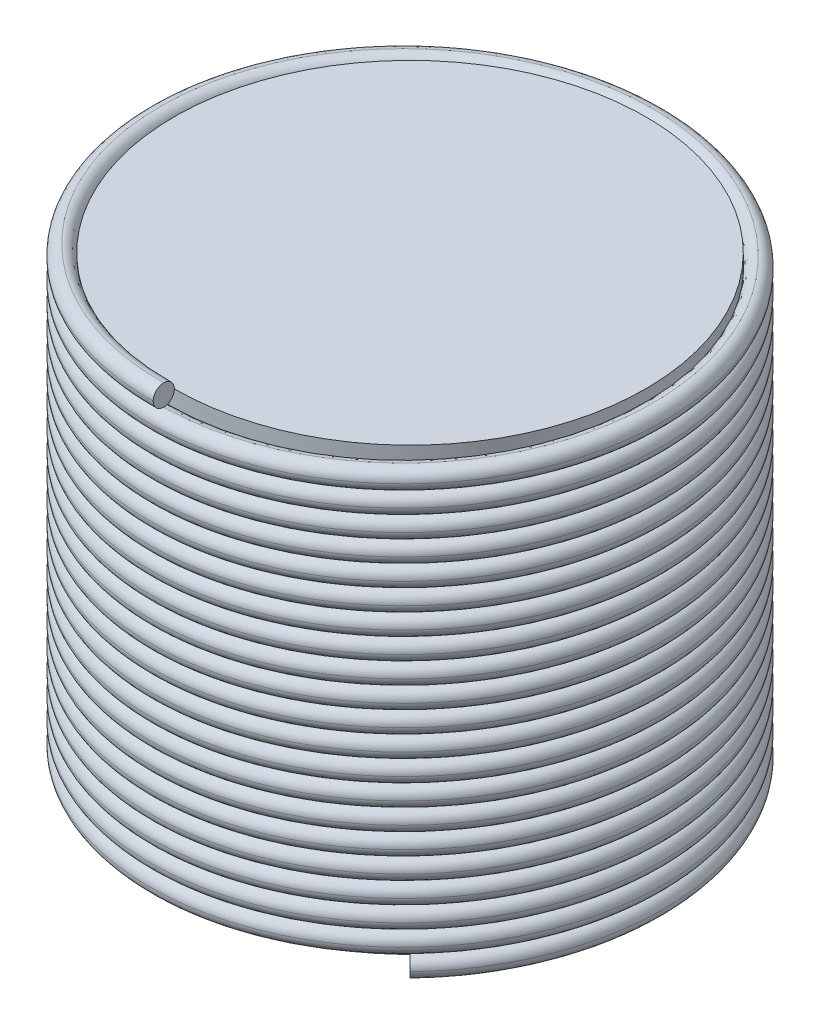
SolidWorks part; units mm, degrees
ref_plane "Front Plane" through (0, 0, 0) normal (0, 0, 1) x (1, 0, 0)
ref_plane "Top Plane" through (0, 0, 0) normal (0, 1, 0) x (1, 0, 0)
ref_plane "Right Plane" through (0, 0, 0) normal (1, 0, 0) x (0, 0, -1)
sketch "Base" plane through (0, 0, 0) normal (0, 1, 0) x (1, 0, 0)
  line L0 (0, 0) -> (0, 12.0382) construction
  line L1 (0, 0) -> (16.2312, 0) construction
  circle A0 centre (0, 0) radius 8.925
  dimension "D1" = 17.85
extrude "Boss-Extrude1" add sketch "Base" along normal blind 16.7 contours A0
sketch "Helix" plane through (0, 16.7, 0) normal (0, 1, 0) x (1, 0, 0)
  circle A0 centre (0, 0) radius 9.325
  circle A1 centre (0, 0) radius 8.925 construction
  dimension "D1" = 0.4
curve "Helix/Spiral1" pitch 0.8 height 16.7 turns 20.875
ref_plane "Start" through (0, 0, 0) normal (1, 0, 0) x (0, 0, -1)
sketch "Winding" plane through (0, 0, 0) normal (1, 0, 0) x (0, 0, -1)
  line L5 (-4.3372, 16.7) -> (-7.5224, 16.7) construction
  line L6 (8.925, 16.7) -> (-8.925, 16.7) construction
  circle A0 centre (-9.325, 16.7) radius 0.4
  spline S0 degree 3 poles (-9.325, 16.7) (-9.325, 16.6834) (-8.8395, 16.65) (-6.7654, 16.6) (-3.6614, 16.55) (0, 16.5) (3.6614, 16.45) (6.7654, 16.4) (8.8395, 16.35) (9.5678, 16.3) (8.8395, 16.25) (6.7654, 16.2) (2.6268, 16.1333) (-2.6268, 16.0667) (-6.7654, 16) (-8.8395, 15.95) (-9.5678, 15.9) (-8.8395, 15.85) (-6.7654, 15.8) (-2.6268, 15.7333) (2.6268, 15.6667) (6.7654, 15.6) (8.8395, 15.55) (9.5678, 15.5) (8.8395, 15.45) (6.7654, 15.4) (2.6268, 15.3333) (-2.6268, 15.2667) (-6.7654, 15.2) (-8.8395, 15.15) (-9.5678, 15.1) (-8.8395, 15.05) (-6.7654, 15) (-2.6268, 14.9333) (2.6268, 14.8667) (6.7654, 14.8) (8.8395, 14.75) (9.5678, 14.7) (8.8395, 14.65) (6.7654, 14.6) (2.6268, 14.5333) (-2.6268, 14.4667) (-6.7654, 14.4) (-8.8395, 14.35) (-9.5678, 14.3) (-8.8395, 14.25) (-6.7654, 14.2) (-2.6268, 14.1333) (2.6268, 14.0667) (6.7654, 14) (8.8395, 13.95) (9.5678, 13.9) (8.8395, 13.85) (6.7654, 13.8) (2.6268, 13.7333) (-2.6268, 13.6667) (-6.7654, 13.6) (-8.8395, 13.55) (-9.5678, 13.5) (-8.8395, 13.45) (-6.7654, 13.4) (-2.6268, 13.3333) (2.6268, 13.2667) (6.7654, 13.2) (8.8395, 13.15) (9.5678, 13.1) (8.8395, 13.05) (6.7654, 13) (2.6268, 12.9333) (-2.6268, 12.8667) (-6.7654, 12.8) (-8.8395, 12.75) (-9.5678, 12.7) (-8.8395, 12.65) (-6.7654, 12.6) (-2.6268, 12.5333) (2.6268, 12.4667) (6.7654, 12.4) (8.8395, 12.35) (9.5678, 12.3) (8.8395, 12.25) (6.7654, 12.2) (2.6268, 12.1333) (-2.6268, 12.0667) (-6.7654, 12) (-8.8395, 11.95) (-9.5678, 11.9) (-8.8395, 11.85) (-6.7654, 11.8) (-2.6268, 11.7333) (2.6268, 11.6667) (6.7654, 11.6) (8.8395, 11.55) (9.5678, 11.5) (8.8395, 11.45) (6.7654, 11.4) (2.6268, 11.3333) (-2.6268, 11.2667) (-6.7654, 11.2) (-8.8395, 11.15) (-9.5678, 11.1) (-8.8395, 11.05) (-6.7654, 11) (-2.6268, 10.9333) (2.6268, 10.8667) (6.7654, 10.8) (8.8395, 10.75) (9.5678, 10.7) (8.8395, 10.65) (6.7654, 10.6) (2.6268, 10.5333) (-2.6268, 10.4667) (-6.7654, 10.4) (-8.8395, 10.35) (-9.5678, 10.3) (-8.8395, 10.25) (-6.7654, 10.2) (-2.6268, 10.1333) (2.6268, 10.0667) (6.7654, 10) (8.8395, 9.95) (9.5678, 9.9) (8.8395, 9.85) (6.7654, 9.8) (2.6268, 9.7333) (-2.6268, 9.6667) (-6.7654, 9.6) (-8.8395, 9.55) (-9.5678, 9.5) (-8.8395, 9.45) (-6.7654, 9.4) (-2.6268, 9.3333) (2.6268, 9.2667) (6.7654, 9.2) (8.8395, 9.15) (9.5678, 9.1) (8.8395, 9.05) (6.7654, 9) (2.6268, 8.9333) (-2.6268, 8.8667) (-6.7654, 8.8) (-8.8395, 8.75) (-9.5678, 8.7) (-8.8395, 8.65) (-6.7654, 8.6) (-2.6268, 8.5333) (2.6268, 8.4667) (6.7654, 8.4) (8.8395, 8.35) (9.5678, 8.3) (8.8395, 8.25) (6.7654, 8.2) (2.6268, 8.1333) (-2.6268, 8.0667) (-6.7654, 8) (-8.8395, 7.95) (-9.5678, 7.9) (-8.8395, 7.85) (-6.7654, 7.8) (-2.6268, 7.7333) (2.6268, 7.6667) (6.7654, 7.6) (8.8395, 7.55) (9.5678, 7.5) (8.8395, 7.45) (6.7654, 7.4) (2.6268, 7.3333) (-2.6268, 7.2667) (-6.7654, 7.2) (-8.8395, 7.15) (-9.5678, 7.1) (-8.8395, 7.05) (-6.7654, 7) (-2.6268, 6.9333) (2.6268, 6.8667) (6.7654, 6.8) (8.8395, 6.75) (9.5678, 6.7) (8.8395, 6.65) (6.7654, 6.6) (2.6268, 6.5333) (-2.6268, 6.4667) (-6.7654, 6.4) (-8.8395, 6.35) (-9.5678, 6.3) (-8.8395, 6.25) (-6.7654, 6.2) (-2.6268, 6.1333) (2.6268, 6.0667) (6.7654, 6) (8.8395, 5.95) (9.5678, 5.9) (8.8395, 5.85) (6.7654, 5.8) (2.6268, 5.7333) (-2.6268, 5.6667) (-6.7654, 5.6) (-8.8395, 5.55) (-9.5678, 5.5) (-8.8395, 5.45) (-6.7654, 5.4) (-2.6268, 5.3333) (2.6268, 5.2667) (6.7654, 5.2) (8.8395, 5.15) (9.5678, 5.1) (8.8395, 5.05) (6.7654, 5) (2.6268, 4.9333) (-2.6268, 4.8667) (-6.7654, 4.8) (-8.8395, 4.75) (-9.5678, 4.7) (-8.8395, 4.65) (-6.7654, 4.6) (-2.6268, 4.5333) (2.6268, 4.4667) (6.7654, 4.4) (8.8395, 4.35) (9.5678, 4.3) (8.8395, 4.25) (6.7654, 4.2) (2.6268, 4.1333) (-2.6268, 4.0667) (-6.7654, 4) (-8.8395, 3.95) (-9.5678, 3.9) (-8.8395, 3.85) (-6.7654, 3.8) (-2.6268, 3.7333) (2.6268, 3.6667) (6.7654, 3.6) (8.8395, 3.55) (9.5678, 3.5) (8.8395, 3.45) (6.7654, 3.4) (2.6268, 3.3333) (-2.6268, 3.2667) (-6.7654, 3.2) (-8.8395, 3.15) (-9.5678, 3.1) (-8.8395, 3.05) (-6.7654, 3) (-2.6268, 2.9333) (2.6268, 2.8667) (6.7654, 2.8) (8.8395, 2.75) (9.5678, 2.7) (8.8395, 2.65) (6.7654, 2.6) (2.6268, 2.5333) (-2.6268, 2.4667) (-6.7654, 2.4) (-8.8395, 2.35) (-9.5678, 2.3) (-8.8395, 2.25) (-6.7654, 2.2) (-2.6268, 2.1333) (2.6268, 2.0667) (6.7654, 2) (8.8395, 1.95) (9.5678, 1.9) (8.8395, 1.85) (6.7654, 1.8) (2.6268, 1.7333) (-2.6268, 1.6667) (-6.7654, 1.6) (-8.8395, 1.55) (-9.5678, 1.5) (-8.8395, 1.45) (-6.7654, 1.4) (-2.6268, 1.3333) (2.6268, 1.2667) (6.7654, 1.2) (8.8395, 1.15) (9.5678, 1.1) (8.8395, 1.05) (6.7654, 1) (2.6268, 0.9333) (-2.6268, 0.8667) (-6.7654, 0.8) (-8.8395, 0.75) (-9.5678, 0.7) (-8.8395, 0.65) (-6.7654, 0.6) (-2.6268, 0.5333) (2.6268, 0.4667) (6.7654, 0.4) (8.8395, 0.35) (9.5678, 0.3) (8.8395, 0.25) (6.7654, 0.2) (3.6616, 0.15) (-0.0007, 0.1) (-3.6589, 0.05) (-5.7362, 0.0166) (-6.5938, 0) knots 0 0 0 0 0.002994 0.005988 0.008982 0.011976 0.01497 0.017964 0.020958 0.023952 0.026946 0.02994 0.032934 0.038922 0.041916 0.04491 0.047904 0.050898 0.053892 0.056886 0.062874 0.065868 0.068862 0.071856 0.07485 0.077844 0.080838 0.086826 0.08982 0.092814 0.095808 0.098802 0.101796 0.10479 0.110778 0.113772 0.116766 0.11976 0.122754 0.125749 0.128743 0.134731 0.137725 0.140719 0.143713 0.146707 0.149701 0.152695 0.158683 0.161677 0.164671 0.167665 0.170659 0.173653 0.176647 0.182635 0.185629 0.188623 0.191617 0.194611 0.197605 0.200599 0.206587 0.209581 0.212575 0.215569 0.218563 0.221557 0.224551 0.230539 0.233533 0.236527 0.239521 0.242515 0.245509 0.248503 0.254491 0.257485 0.260479 0.263473 0.266467 0.269461 0.272455 0.278443 0.281437 0.284431 0.287425 0.290419 0.293413 0.296407 0.302395 0.305389 0.308383 0.311377 0.314371 0.317365 0.320359 0.326347 0.329341 0.332335 0.335329 0.338323 0.341317 0.344311 0.350299 0.353293 0.356287 0.359281 0.362275 0.365269 0.368263 0.374251 0.377246 0.38024 0.383234 0.386228 0.389222 0.392216 0.398204 0.401198 0.404192 0.407186 0.41018 0.413174 0.416168 0.422156 0.42515 0.428144 0.431138 0.434132 0.437126 0.44012 0.446108 0.449102 0.452096 0.45509 0.458084 0.461078 0.464072 0.47006 0.473054 0.476048 0.479042 0.482036 0.48503 0.488024 0.494012 0.497006 0.5 0.502994 0.505988 0.508982 0.511976 0.517964 0.520958 0.523952 0.526946 0.52994 0.532934 0.535928 0.541916 0.54491 0.547904 0.550898 0.553892 0.556886 0.55988 0.565868 0.568862 0.571856 0.57485 0.577844 0.580838 0.583832 0.58982 0.592814 0.595808 0.598802 0.601796 0.60479 0.607784 0.613772 0.616766 0.61976 0.622754 0.625749 0.628743 0.631737 0.637725 0.640719 0.643713 0.646707 0.649701 0.652695 0.655689 0.661677 0.664671 0.667665 0.670659 0.673653 0.676647 0.679641 0.685629 0.688623 0.691617 0.694611 0.697605 0.700599 0.703593 0.709581 0.712575 0.715569 0.718563 0.721557 0.724551 0.727545 0.733533 0.736527 0.739521 0.742515 0.745509 0.748503 0.751497 0.757485 0.760479 0.763473 0.766467 0.769461 0.772455 0.775449 0.781437 0.784431 0.787425 0.790419 0.793413 0.796407 0.799401 0.805389 0.808383 0.811377 0.814371 0.817365 0.820359 0.823353 0.829341 0.832335 0.835329 0.838323 0.841317 0.844311 0.847305 0.853293 0.856287 0.859281 0.862275 0.865269 0.868263 0.871257 0.877246 0.88024 0.883234 0.886228 0.889222 0.892216 0.89521 0.901198 0.904192 0.907186 0.91018 0.913174 0.916168 0.919162 0.92515 0.928144 0.931138 0.934132 0.937126 0.94012 0.943114 0.949102 0.952096 0.95509 0.958084 0.961078 0.964072 0.967066 0.973054 0.976048 0.979042 0.982036 0.98503 0.988024 0.991018 0.994012 0.997006 1 1 1 1 construction
  point P0 (-9.325, 16.7)
  dimension "D1" = 0.8
sweep "Sweep1" add profiles "Winding" path "Helix/Spiral1"
equation "\"Coil_Diameter\"= \"Bore@Coil.Assembly\" + 5"
equation "\"D1@Base\" = \"Coil_Diameter\""
equation "\"Coil_Height\"= \"Coil_Height@Coil.Assembly\" - 2.5 - \"Wire_Guage\""
equation "\"D1@Boss-Extrude1\"=\"Coil_Height\""
equation "\"Wire_Guage\"=0.8"
equation "\"D1@Winding\"=\"Wire_Guage\""
